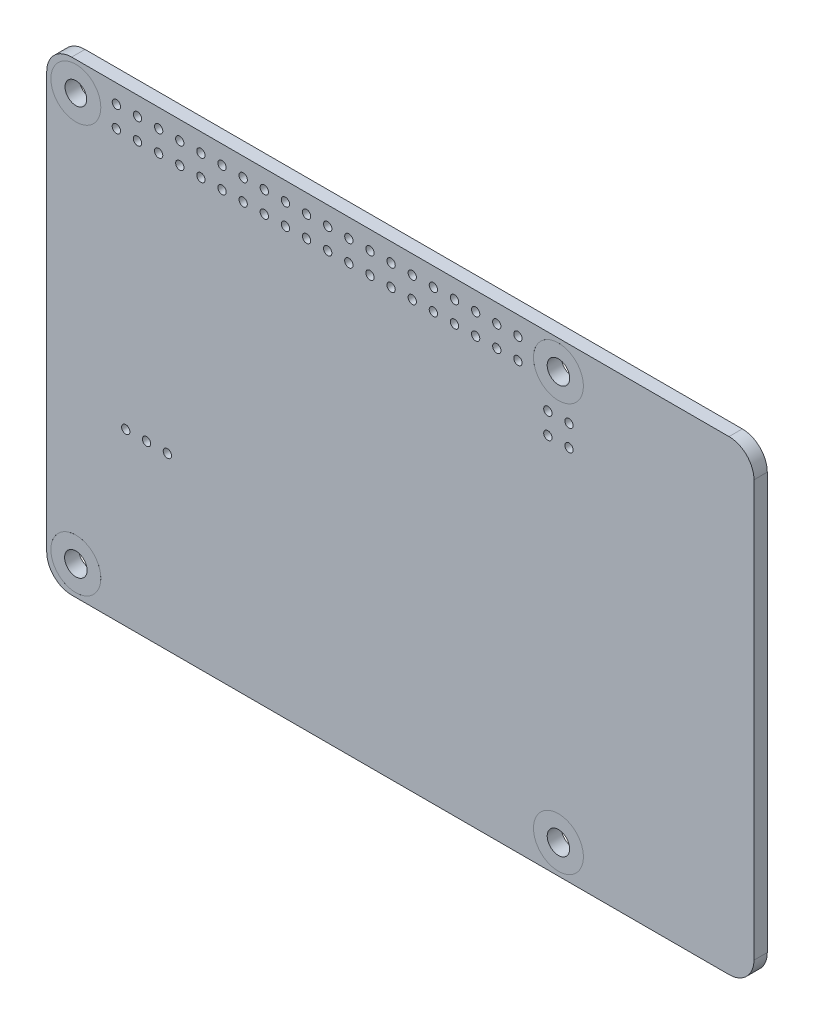
SolidWorks part; units mm, degrees
ref_plane "Płaszczyzna przednia" through (0, 0, 0) normal (0, 0, 1) x (1, 0, 0)
ref_plane "Płaszczyzna górna" through (0, 0, 0) normal (0, 1, 0) x (1, 0, 0)
ref_plane "Płaszczyzna prawa" through (0, 0, 0) normal (1, 0, 0) x (0, 0, -1)
sketch "Sketch1" plane through (0, 0, 0) normal (0, 0, 1) x (1, 0, 0)
  line L0 (-39.5, -28) -> (39.5, -28)
  line L1 (42.5, -25) -> (42.5, 25)
  line L2 (39.5, 28) -> (-39.5, 28)
  line L3 (-42.5, 25) -> (-42.5, -25)
  line L4 (0, -28) -> (0, 28) construction
  arc A0 (39.5, -28) -> (42.5, -25) centre (39.5, -25) ccw
  arc A1 (42.5, 25) -> (39.5, 28) centre (39.5, 25) ccw
  arc A2 (-39.5, 28) -> (-42.5, 25) centre (-39.5, 25) ccw
  arc A3 (-42.5, -25) -> (-39.5, -28) centre (-39.5, -25) ccw
  dimension "D3" = 3
  dimension "D1" = 85
  dimension "D2" = 56
extrude "Boss-Extrude1" add sketch "Sketch1" along normal blind 1.6
sketch "Sketch3" plane through (0, 0, 1.6) normal (0, 0, 1) x (1, 0, 0)
  line L0 (-39, 28) -> (-39, 24.5) construction
  line L1 (39.5, 28) -> (-39.5, 28) construction
  line L2 (-39, 24.5) -> (-42.5, 24.5) construction
  line L4 (-42.5, 25) -> (-42.5, -25) construction
  line L5 (-42.5, 0) -> (-59.0247, 0) construction
  line L6 (-39, -24.5) -> (-42.5, -24.5) construction
  line L7 (-39, -28) -> (-39, -24.5) construction
  line L8 (-39, 24.5) -> (19, 24.5) construction
  line L9 (-10, 24.5) -> (-10, 38.9461) construction
  line L10 (19, -28) -> (19, -24.5) construction
  line L11 (19, -24.5) -> (22.5, -24.5) construction
  line L12 (22.5, 0) -> (39.0247, 0) construction
  line L13 (19, 24.5) -> (22.5, 24.5) construction
  line L14 (19, 28) -> (19, 24.5) construction
  circle A1 centre (-39, 24.5) radius 3
  circle A2 centre (-39, -24.5) radius 3
  circle A3 centre (19, -24.5) radius 3
  circle A4 centre (19, 24.5) radius 3
  dimension "D1" = 3.5
  dimension "D2" = 3.5
extrude "Cut-Extrude1" cut sketch "Sketch3" against normal through all
sketch "Sketch4" plane through (0, 0, 1.6) normal (0, 0, 1) x (1, 0, 0)
  circle A0 centre (-39, -24.5) radius 3 construction
  circle A1 centre (19, -24.5) radius 3 construction
  circle A2 centre (19, 24.5) radius 3 construction
  circle A3 centre (-39, 24.5) radius 3 construction
  circle A4 centre (-39, -24.5) radius 3
  circle A5 centre (19, -24.5) radius 3
  circle A6 centre (19, 24.5) radius 3
  circle A7 centre (-39, 24.5) radius 3
  circle A8 centre (-39, -24.5) radius 1.35
  circle A9 centre (19, -24.5) radius 1.35
  circle A10 centre (19, 24.5) radius 1.35
  circle A11 centre (-39, 24.5) radius 1.3
  dimension "D1" = 2.6
extrude "Boss-Extrude2" add sketch "Sketch4" against normal blind 1.7 separate body
sketch "Sketch5" plane through (0, 0, 1.6) normal (0, 0, 1) x (1, 0, 0)
  line L0 (-33, -28) -> (-33, -7.5) construction
  line L1 (-39.5, -28) -> (39.5, -28) construction
  line L2 (-42.5, -7.5) -> (-33, -7.5) construction
  line L3 (-42.5, 25) -> (-42.5, -25) construction
  line L4 (-33, -7.5) -> (-30.5, -7.5) construction
  line L5 (-30.5, -7.5) -> (-28, -7.5) construction
  circle A0 centre (-33, -7.5) radius 0.5
  circle A1 centre (-30.5, -7.5) radius 0.5
  circle A2 centre (-28, -7.5) radius 0.5
  dimension "D1" = 9.5
  dimension "D2" = 20.5
extrude "Cut-Extrude2" cut sketch "Sketch5" against normal through all
sketch "Sketch6" plane through (0, 0, 1.6) normal (0, 0, 1) x (1, 0, 0)
  line L0 (39.5, 28) -> (-39.5, 28) construction
  line L1 (-42.5, 25) -> (-42.5, -25) construction
  circle A0 centre (-34.13, 25.77) radius 0.5
  circle A1 centre (-34.13, 23.23) radius 0.5
  circle A2 centre (-31.59, 25.77) radius 0.5
  circle A3 centre (-31.59, 23.23) radius 0.5
  circle A4 centre (-29.05, 25.77) radius 0.5
  circle A5 centre (-29.05, 23.23) radius 0.5
  circle A6 centre (-26.51, 25.77) radius 0.5
  circle A7 centre (-26.51, 23.23) radius 0.5
  circle A8 centre (-23.97, 25.77) radius 0.5
  circle A9 centre (-23.97, 23.23) radius 0.5
  circle A10 centre (-21.43, 25.77) radius 0.5
  circle A11 centre (-21.43, 23.23) radius 0.5
  circle A12 centre (-18.89, 25.77) radius 0.5
  circle A13 centre (-18.89, 23.23) radius 0.5
  circle A14 centre (-16.35, 25.77) radius 0.5
  circle A15 centre (-16.35, 23.23) radius 0.5
  circle A16 centre (-13.81, 25.77) radius 0.5
  circle A17 centre (-13.81, 23.23) radius 0.5
  circle A18 centre (-11.27, 25.77) radius 0.5
  circle A19 centre (-11.27, 23.23) radius 0.5
  circle A20 centre (-8.73, 25.77) radius 0.5
  circle A21 centre (-8.73, 23.23) radius 0.5
  circle A22 centre (-6.19, 25.77) radius 0.5
  circle A23 centre (-6.19, 23.23) radius 0.5
  circle A24 centre (-3.65, 25.77) radius 0.5
  circle A25 centre (-3.65, 23.23) radius 0.5
  circle A26 centre (-1.11, 25.77) radius 0.5
  circle A27 centre (-1.11, 23.23) radius 0.5
  circle A28 centre (1.43, 25.77) radius 0.5
  circle A29 centre (1.43, 23.23) radius 0.5
  circle A30 centre (3.97, 25.77) radius 0.5
  circle A31 centre (3.97, 23.23) radius 0.5
  circle A32 centre (6.51, 25.77) radius 0.5
  circle A33 centre (6.51, 23.23) radius 0.5
  circle A34 centre (9.05, 25.77) radius 0.5
  circle A35 centre (9.05, 23.23) radius 0.5
  circle A36 centre (11.59, 25.77) radius 0.5
  circle A37 centre (11.59, 23.23) radius 0.5
  circle A38 centre (14.13, 25.77) radius 0.5
  circle A39 centre (14.13, 23.23) radius 0.5
  dimension "D1" = 2.54
  dimension "D2" = 1
  dimension "D3" = 2.23
  dimension "D4" = 8.37
  dimension "D5" = 20
extrude "Cut-Extrude3" cut sketch "Sketch6" against normal through all
sketch "Sketch7" plane through (0, 0, 1.6) normal (0, 0, 1) x (1, 0, 0)
  line L0 (42.5, -25) -> (42.5, 25) construction
  line L1 (39.5, 28) -> (-39.5, 28) construction
  circle A0 centre (20.27, 19.77) radius 0.5
  circle A1 centre (17.73, 19.77) radius 0.5
  circle A2 centre (17.73, 17.23) radius 0.5
  circle A3 centre (20.27, 17.23) radius 0.5
  dimension "D1" = 22.23
  dimension "D2" = 8.23
  dimension "D3" = 2.54
  dimension "D4" = 2.54
  dimension "D5" = 1
extrude "Cut-Extrude4" cut sketch "Sketch7" against normal through all
